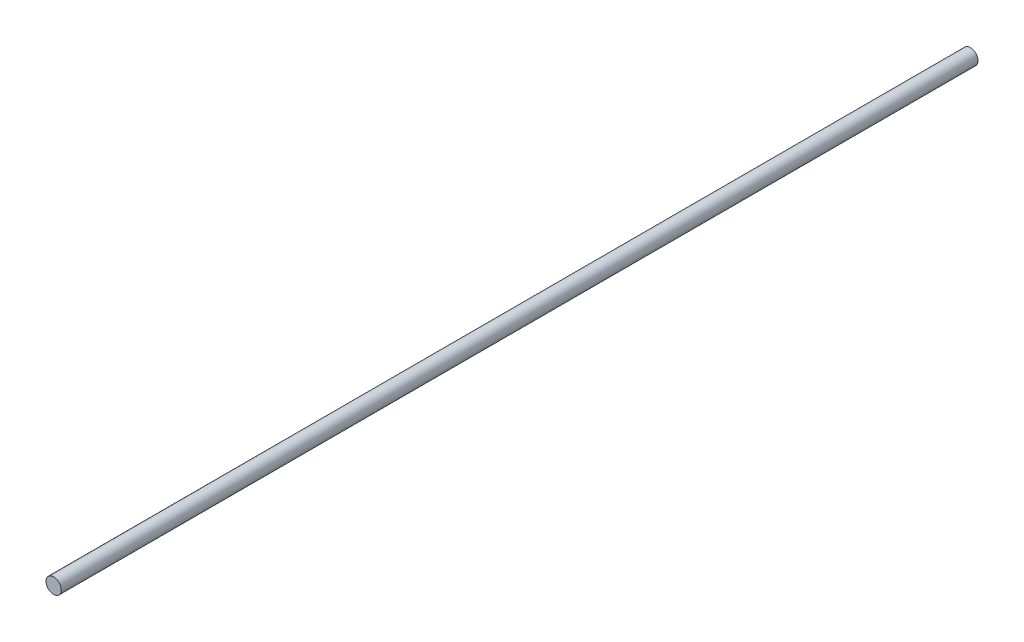
SolidWorks part; units mm, degrees
ref_plane "Front Plane" through (0, 0, 0) normal (0, 0, 1) x (1, 0, 0)
ref_plane "Top Plane" through (0, 0, 0) normal (0, 1, 0) x (1, 0, 0)
ref_plane "Right Plane" through (0, 0, 0) normal (1, 0, 0) x (0, 0, -1)
sketch "Sketch1" plane through (0, 0, 0) normal (0, 0, 1) x (1, 0, 0)
  circle A0 centre (0, 0) radius 2.5
extrude "Boss-Extrude1" add sketch "Sketch1" along normal blind 300
